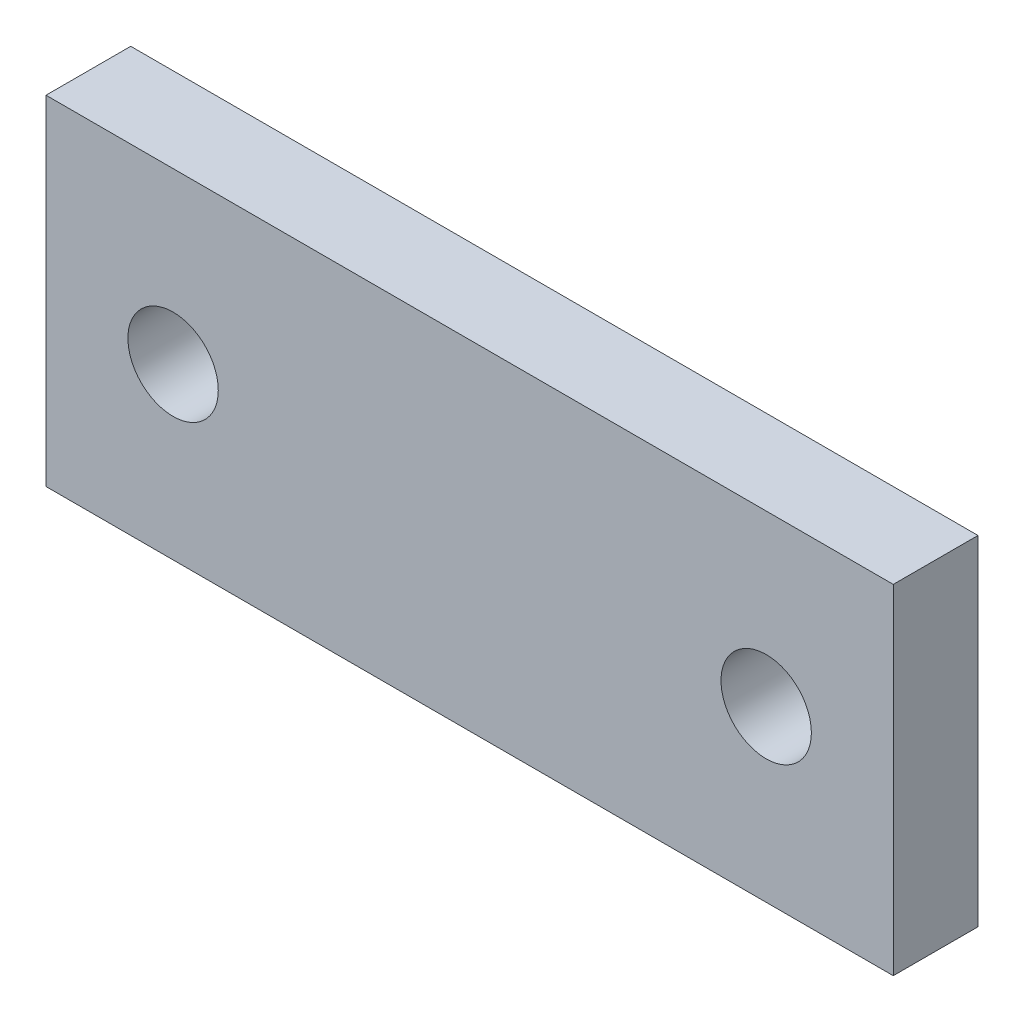
SolidWorks part; units mm, degrees
ref_plane "Front Plane" through (0, 0, 0) normal (0, 0, 1) x (1, 0, 0)
ref_plane "Top Plane" through (0, 0, 0) normal (0, 1, 0) x (1, 0, 0)
ref_plane "Right Plane" through (0, 0, 0) normal (1, 0, 0) x (0, 0, -1)
sketch "Sketch1" plane through (0, 0, 0) normal (0, 0, 1) x (1, 0, 0)
  line L1 (24.7194, 0) -> (-5.2806, 0)
  line L2 (24.7194, 0) -> (24.7194, 12)
  line L3 (24.7194, 12) -> (-5.2806, 12)
  line L4 (-5.2806, 0) -> (-5.2806, 12)
  circle A0 centre (-0.7806, 6) radius 1.6
  circle A1 centre (20.2194, 6) radius 1.6
  dimension "D1" = 3.2
extrude "Boss-Extrude1" add sketch "Sketch1" along normal blind 3
